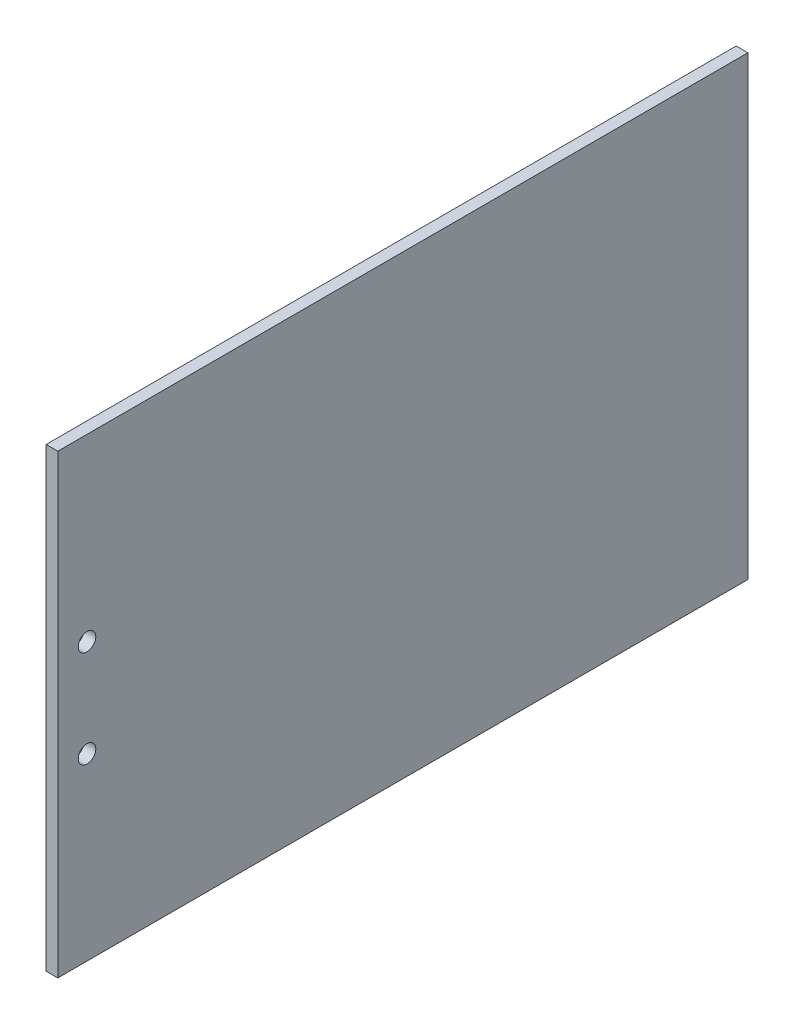
SolidWorks part; units mm, degrees
ref_plane "Front Plane" through (0, 0, 0) normal (0, 0, 1) x (1, 0, 0)
ref_plane "Top Plane" through (0, 0, 0) normal (0, 1, 0) x (1, 0, 0)
ref_plane "Right Plane" through (0, 0, 0) normal (1, 0, 0) x (0, 0, -1)
sketch "Sketch1" plane through (0, 0, 0) normal (1, 0, 0) x (0, 0, -1)
  line L0 (0, 0) -> (-74.93, 0) construction
  line L1 (74.93, 49.53) -> (-74.93, 49.53)
  line L2 (74.93, 49.53) -> (74.93, -49.53)
  line L3 (74.93, -49.53) -> (-74.93, -49.53)
  line L4 (-74.93, 49.53) -> (-74.93, -49.53)
  line L5 (74.93, 49.53) -> (-74.93, -49.53) construction
  line L6 (74.93, -49.53) -> (-74.93, 49.53) construction
  line L7 (-68.58, 10.541) -> (-68.58, -10.541) construction
  circle A0 centre (-68.58, 10.541) radius 1.905
  circle A1 centre (-68.58, -10.541) radius 1.905
  point P0 (0, 0)
  point P11 (-68.58, 0)
  dimension "D3" = 3.81
  dimension "D4" = 3.81
  dimension "D1" = 149.86
  dimension "D2" = 99.06
  dimension "D5" = 21.082
  dimension "D6" = 6.35
extrude "Boss-Extrude1" add sketch "Sketch1" along normal blind 2.54
